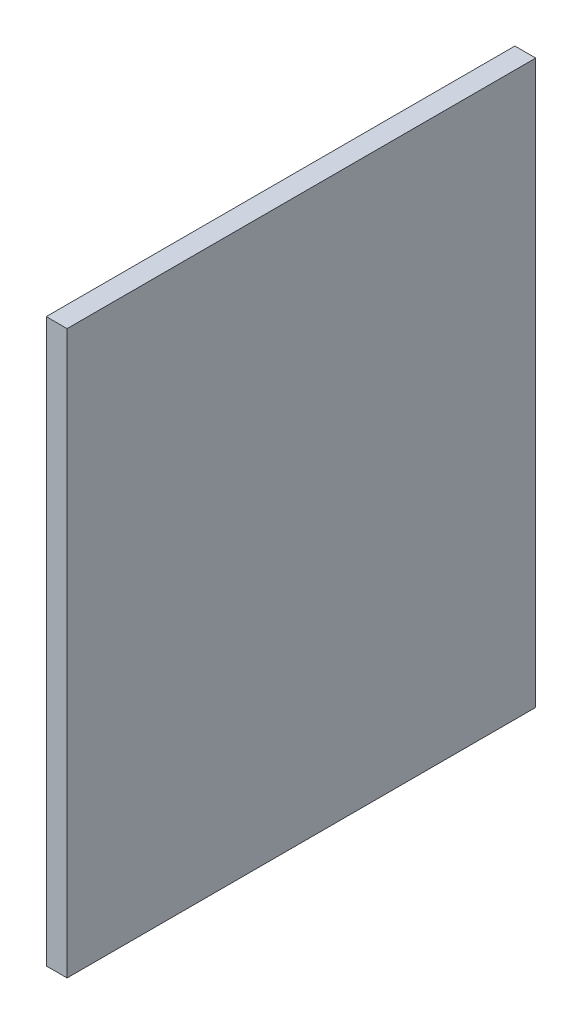
SolidWorks part; units mm, degrees
ref_plane "Alzado" through (0, 0, 0) normal (0, 0, 1) x (1, 0, 0)
ref_plane "Planta" through (0, 0, 0) normal (0, 1, 0) x (1, 0, 0)
ref_plane "Vista lateral" through (0, 0, 0) normal (1, 0, 0) x (0, 0, -1)
sketch "Croquis2" plane through (0, 0, 0) normal (1, 0, 0) x (0, 0, -1)
  line L1 (-67.5, 81) -> (67.5, 81)
  line L2 (-67.5, 81) -> (-67.5, -81)
  line L3 (-67.5, -81) -> (67.5, -81)
  line L4 (67.5, 81) -> (67.5, -81)
  line L5 (-67.5, 81) -> (67.5, -81) construction
  line L6 (-67.5, -81) -> (67.5, 81) construction
  point P0 (0, 0)
  dimension "D1" = 135
  dimension "D2" = 162
extrude "Saliente-Extruir1" add sketch "Croquis2" along normal blind 6
